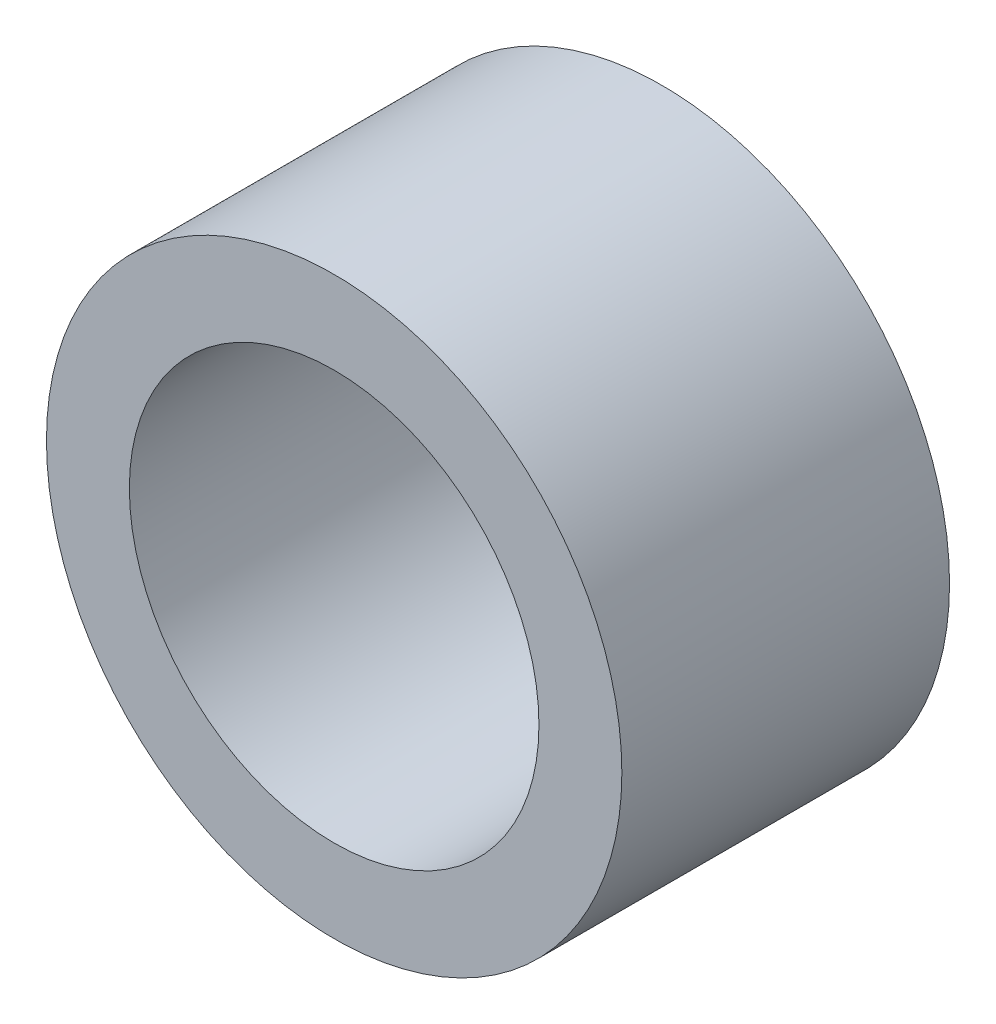
SolidWorks part; units mm, degrees
ref_plane "Front Plane" through (0, 0, 0) normal (0, 0, 1) x (1, 0, 0)
ref_plane "Top Plane" through (0, 0, 0) normal (0, 1, 0) x (1, 0, 0)
ref_plane "Right Plane" through (0, 0, 0) normal (1, 0, 0) x (0, 0, -1)
sketch "Sketch1" plane through (0, 0, 0) normal (0, 0, 1) x (1, 0, 0)
  circle A0 centre (0, 0) radius 5.5753
  circle A1 centre (0, 0) radius 3.9688
  dimension "D1" = 11.1506
  dimension "ID" = 7.9375
extrude "Extrude1" add sketch "Sketch1" along normal mid plane 6.35
sketch "Sketch2" plane through (0, 0, 0) normal (1, 0, 0) x (0, 0, -1)
  line L0 (-3.175, -3.9688) -> (3.175, -3.9688) construction
  line L3 (3.175, 3.9688) -> (-3.175, 3.9688) construction
  line L5 (-3.175, -3.9688) -> (3.175, -3.9688)
  line L6 (3.175, 3.9688) -> (-3.175, 3.9688)
sketch "Sketch4" plane through (0, 0, 3.175) normal (0, 0, 1) x (1, 0, 0)
  line L0 (0, 0) -> (-2.8063, 2.8063)
  line L1 (0, -3.4925) -> (0, 3.4925) construction
  circle A0 centre (0, 0) radius 3.9688 construction
  dimension "D1" = 45
